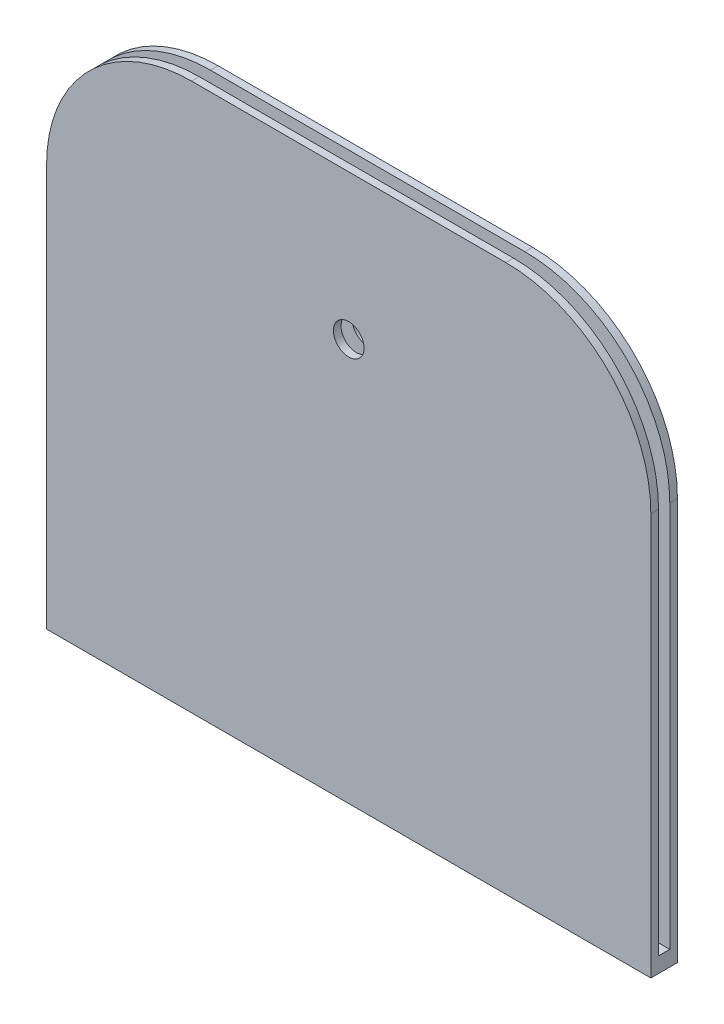
SolidWorks part; units mm, degrees
ref_plane "Alzado" through (0, 0, 0) normal (0, 0, 1) x (1, 0, 0)
ref_plane "Planta" through (0, 0, 0) normal (0, 1, 0) x (1, 0, 0)
ref_plane "Vista lateral" through (0, 0, 0) normal (1, 0, 0) x (0, 0, -1)
sketch "Croquis1" plane through (0, 0, 0) normal (0, 1, 0) x (1, 0, 0)
  line L1 (0, 5.1912) -> (250, 5.1912)
  line L2 (0, 5.1912) -> (0, -5.8088)
  line L3 (0, -5.8088) -> (250, -5.8088)
  line L4 (250, 5.1912) -> (250, -5.8088)
  dimension "D1" = 250
  dimension "D2" = 11
extrude "Saliente-Extruir1" add sketch "Croquis1" along normal blind 6.35
sketch "Croquis2" plane through (0, 6.35, 0) normal (0, 1, 0) x (1, 0, 0)
  line L0 (0, 5.1912) -> (0, -5.8088) construction
  line L1 (250, 5.1912) -> (0, 5.1912)
  line L2 (250, 5.1912) -> (250, 2.0162)
  line L3 (250, 2.0162) -> (0, 2.0162)
  line L4 (0, 5.1912) -> (0, 2.0162)
  line L5 (250, -5.8088) -> (250, 5.1912) construction
  line L6 (0, -5.8088) -> (250, -5.8088)
  line L7 (0, -5.8088) -> (0, -2.6338)
  line L8 (0, -2.6338) -> (250, -2.6338)
  line L9 (250, -5.8088) -> (250, -2.6338)
  dimension "D1" = 3.175
  dimension "D2" = 3.175
extrude "Saliente-Extruir2" add sketch "Croquis2" along normal blind 220
fillet "Redondeo1" radius 60 4 edges at (250, 226.35, 4.2213) (250, 226.35, -3.6037) (0, 226.35, -3.6037) (0, 226.35, 4.2213)
sketch "Croquis4" plane through (0, 0, -5.1912) normal (0, 0, -1) x (-1, 0, 0)
  line L0 (-125, 226.35) -> (-125, 166.35) construction
  line L1 (-190, 226.35) -> (-60, 226.35) construction
  circle A0 centre (-125, 166.35) radius 6.35
  dimension "D2" = 12.7
  dimension "D1" = 60
extrude "Cortar-Extruir1" cut sketch "Croquis4" against normal up to surface (11 mm away) up to face at (125, 135.0421, 5.8088)
